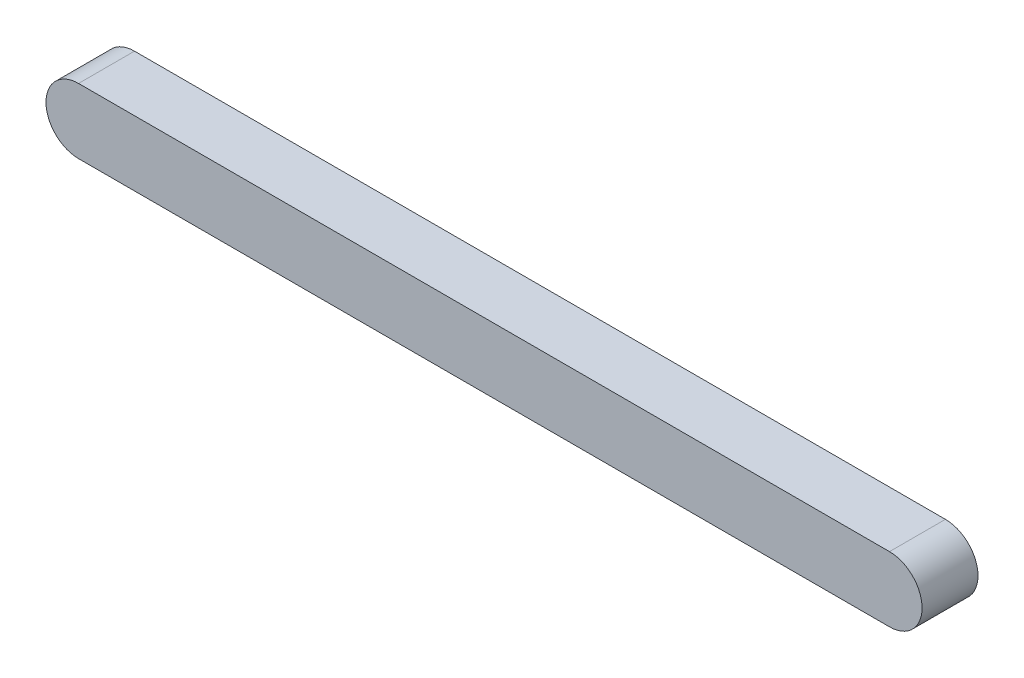
SolidWorks part; units mm, degrees
ref_plane "前视基准面" through (0, 0, 0) normal (0, 0, 1) x (1, 0, 0)
ref_plane "上视基准面" through (0, 0, 0) normal (0, 1, 0) x (1, 0, 0)
ref_plane "右视基准面" through (0, 0, 0) normal (1, 0, 0) x (0, 0, -1)
sketch "草图1" plane through (0, 0, 0) normal (0, 0, 1) x (1, 0, 0)
  line L0 (-145, 0) -> (0, 0) construction
  line L1 (-145, 5.8253) -> (0, 5.8253)
  line L2 (-145, -5.8253) -> (0, -5.8253)
  arc A0 (-145, 5.8253) -> (-145, -5.8253) centre (-145, 0) ccw
  arc A1 (0, -5.8253) -> (0, 5.8253) centre (0, 0) ccw
  point P2 (-72.5, 0)
  dimension "D1" = 145
  dimension "D2" = 11.6506
extrude "凸台-拉伸1" add sketch "草图1" along normal blind 10
